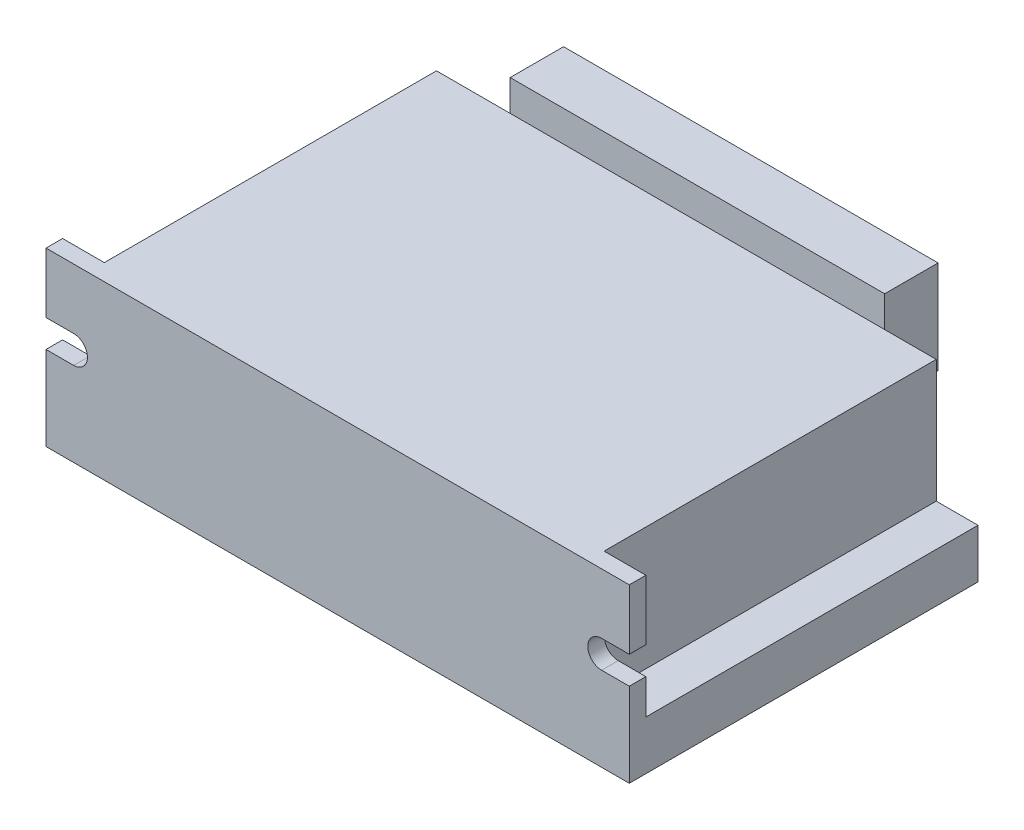
SolidWorks part; units mm, degrees
ref_plane "前视基准面" through (0, 0, 0) normal (0, 0, 1) x (1, 0, 0)
ref_plane "上视基准面" through (0, 0, 0) normal (0, 1, 0) x (1, 0, 0)
ref_plane "右视基准面" through (0, 0, 0) normal (1, 0, 0) x (0, 0, -1)
sketch "草图1" plane through (0, 0, 0) normal (1, 0, 0) x (0, 0, -1)
  line L0 (0, 0) -> (-56.8, 0)
  line L1 (-56.8, 0) -> (-56.8, 28)
  line L2 (-56.8, 28) -> (-54.1, 28)
  line L3 (-54.1, 28) -> (-54.1, 8)
  line L4 (-54.1, 8) -> (0, 8)
  line L5 (0, 8) -> (0, 0)
  dimension "D1" = 8
  dimension "D2" = 56.8
  dimension "D3" = 28
  dimension "D4" = 2.7
extrude "凸台-拉伸1" add sketch "草图1" along normal blind 95
sketch "草图2" plane through (0, 8, 0) normal (0, 1, 0) x (1, 0, 0)
  line L0 (95, -54.1) -> (0, -54.1) construction
  line L1 (6.8, -54.1) -> (88.2, -54.1)
  line L2 (6.8, -54.1) -> (6.8, 0)
  line L3 (6.8, 0) -> (88.2, 0)
  line L4 (88.2, -54.1) -> (88.2, 0)
  line L5 (95, 0) -> (0, 0) construction
  line L6 (0, 0) -> (0, -54.1) construction
  line L7 (95, 0) -> (95, -54.1) construction
  dimension "D1" = 6.8
  dimension "D2" = 6.8
extrude "凸台-拉伸2" add sketch "草图2" along normal blind 20
sketch "草图3" plane through (0, 0, 0) normal (0, 0, -1) x (-1, 0, 0)
  line L0 (-88.2, 28) -> (-88.2, 8) construction
  line L1 (-75.5, 13.5536) -> (-14.5, 13.5536)
  line L2 (-75.5, 13.5536) -> (-75.5, 21.5536)
  line L3 (-75.5, 21.5536) -> (-14.5, 21.5536)
  line L4 (-14.5, 13.5536) -> (-14.5, 21.5536)
  dimension "D1" = 8
  dimension "D2" = 61
  dimension "D3" = 12.7
extrude "凸台-拉伸3" add sketch "草图3" along normal blind 13
sketch "草图4" plane through (0, 21.5536, 0) normal (0, 1, 0) x (1, 0, 0)
  line L0 (14.5, 13) -> (14.5, 0) construction
  line L1 (14.5, 4.3) -> (75.5, 4.3)
  line L2 (14.5, 4.3) -> (14.5, 13)
  line L3 (14.5, 13) -> (75.5, 13)
  line L4 (75.5, 4.3) -> (75.5, 13)
  dimension "D1" = 8.7
extrude "凸台-拉伸4" add sketch "草图4" along normal blind 7.2
sketch "草图7" plane through (0, 0, 56.8) normal (0, 0, 1) x (1, 0, 0)
  line L0 (4.5, 18.2) -> (0, 18.2)
  line L1 (0, 28) -> (0, 0) construction
  line L2 (4.5, 13.7) -> (0, 13.7)
  line L3 (0, 13.7) -> (0, 18.2)
  line L4 (95, 28) -> (0, 28) construction
  line L5 (47.5, 0) -> (47.5, 41.1256) construction
  line L6 (95, 0) -> (0, 0) construction
  line L7 (90.5, 13.7) -> (95, 13.7)
  line L8 (95, 13.7) -> (95, 18.2)
  line L9 (90.5, 18.2) -> (95, 18.2)
  arc A0 (4.5, 13.7) -> (4.5, 18.2) centre (4.5, 15.95) ccw
  arc A1 (90.5, 13.7) -> (90.5, 18.2) centre (90.5, 15.95) cw
  dimension "D1" = 4.5
  dimension "D2" = 9.8
  dimension "D3" = 4.5
extrude "切除-拉伸1" cut sketch "草图7" against normal through all
